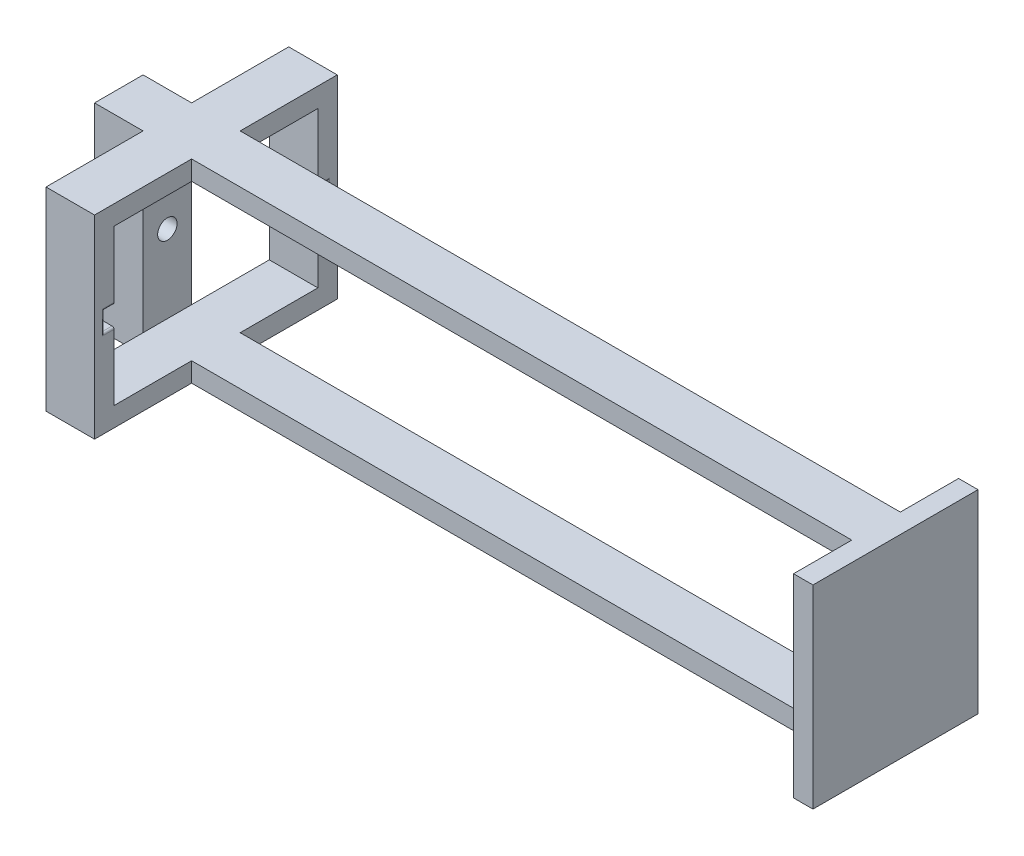
SolidWorks part; units mm, degrees
ref_plane "Front Plane" through (0, 0, 0) normal (0, 0, 1) x (1, 0, 0)
ref_plane "Top Plane" through (0, 0, 0) normal (0, 1, 0) x (1, 0, 0)
ref_plane "Right Plane" through (0, 0, 0) normal (1, 0, 0) x (0, 0, -1)
sketch "Sketch1" plane through (0, 0, 0) normal (0, 0, 1) x (1, 0, 0)
  line L1 (0, 12.7) -> (101.6, 12.7)
  line L2 (0, 12.7) -> (0, -12.7)
  line L3 (0, -12.7) -> (101.6, -12.7)
  line L5 (101.6, -12.7) -> (101.6, 12.7)
  point P4 (0, 0)
  dimension "D3" = 25.4
  dimension "D4" = 101.6
extrude "Boss-Extrude1" add sketch "Sketch1" along normal mid plane 6.35
ref_plane "Plane1" through (12.7, 0, 0) normal (-1, 0, 0) x (0, 0, 1)
sketch "Sketch2" plane through (12.7, 0, 0) normal (-1, 0, 0) x (0, 0, 1)
  line L0 (-3.175, 12.7) -> (-15.875, 12.7)
  line L1 (-15.875, 12.7) -> (-15.875, -12.7)
  line L2 (-15.875, -12.7) -> (-3.175, -12.7)
  line L3 (-3.175, -12.7) -> (-3.175, -10.16)
  line L4 (-3.175, 12.7) -> (-3.175, -12.7) construction
  line L5 (-3.175, -10.16) -> (-13.335, -10.16)
  line L6 (-13.335, -10.16) -> (-13.335, 10.16)
  line L7 (-13.335, 10.16) -> (-3.175, 10.16)
  line L8 (-3.175, 12.7) -> (-3.175, 10.16)
  dimension "D1" = 12.7
  dimension "D2" = 2.54
  dimension "D3" = 10.16
  dimension "D4" = 2.54
extrude "Boss-Extrude2" add sketch "Sketch2" along normal blind 6.35
sketch "Sketch4" plane through (0, 0, -13.335) normal (0, 0, 1) x (1, 0, 0)
  line L0 (12.7, 3.4925) -> (12.7, -3.4925) construction
  line L1 (6.35, 1.27) -> (12.7, 1.27)
  line L2 (6.35, 1.27) -> (6.35, -1.27)
  line L3 (6.35, -1.27) -> (12.7, -1.27)
  line L4 (12.7, 1.27) -> (12.7, -1.27)
  line L5 (6.35, 1.27) -> (12.7, -1.27) construction
  line L6 (6.35, -1.27) -> (12.7, 1.27) construction
  line L7 (6.35, -10.16) -> (6.35, 10.16) construction
  point P0 (9.525, 0)
  dimension "D1" = 2.54
extrude "Cut-Extrude2" cut sketch "Sketch4" against normal blind 1.27
fillet "Fillet2" radius 0.254 3 edges at (6.35, 0, -14.605) (6.35, -1.27, -13.97) (6.35, 1.27, -13.97)
fillet "Fillet3" radius 0.254 3 edges at (12.7, 0, -14.605) (12.7, 1.27, -13.97) (12.7, -1.27, -13.97)
mirror "Mirror4" about plane through (0, 0, 0) normal (0, 0, 1) of "Fillet3", "Fillet2", "Cut-Extrude2", "Boss-Extrude2"
sketch "Sketch6" plane through (101.6, 0, 0) normal (1, 0, 0) x (0, 0, -1)
  line L1 (3.175, 12.7) -> (10.795, 12.7)
  line L2 (3.175, 12.7) -> (3.175, -12.7)
  line L3 (3.175, -12.7) -> (10.795, -12.7)
  line L4 (10.795, 12.7) -> (10.795, -12.7)
  dimension "D1" = 7.62
extrude "Boss-Extrude4" add sketch "Sketch6" against normal blind 2.54
mirror "Mirror5" about plane through (0, 0, 0) normal (0, 0, 1) of "Boss-Extrude4"
sketch "Sketch7" plane through (0, 0, 3.175) normal (0, 0, 1) x (1, 0, 0)
  line L0 (99.06, 12.7) -> (99.06, -12.7) construction
  line L1 (6.35, 10.16) -> (99.06, 10.16)
  line L2 (6.35, 10.16) -> (6.35, -10.16)
  line L3 (6.35, -10.16) -> (99.06, -10.16)
  line L4 (99.06, 10.16) -> (99.06, -10.16)
  line L5 (6.35, 10.16) -> (99.06, -10.16) construction
  line L6 (6.35, -10.16) -> (99.06, 10.16) construction
  line L7 (0, 12.7) -> (0, -12.7) construction
  line L8 (99.06, 12.7) -> (12.7, 12.7) construction
  point P0 (52.705, 0)
  dimension "D1" = 6.35
  dimension "D2" = 2.54
extrude "Cut-Extrude3" cut sketch "Sketch7" against normal up to next
sketch "Sketch8" plane through (0, 0, 0) normal (-1, 0, 0) x (0, 0, 1)
  circle A0 centre (0, 0) radius 1.27
  dimension "D1" = 2.54
extrude "Cut-Extrude4" cut sketch "Sketch8" against normal up to next
